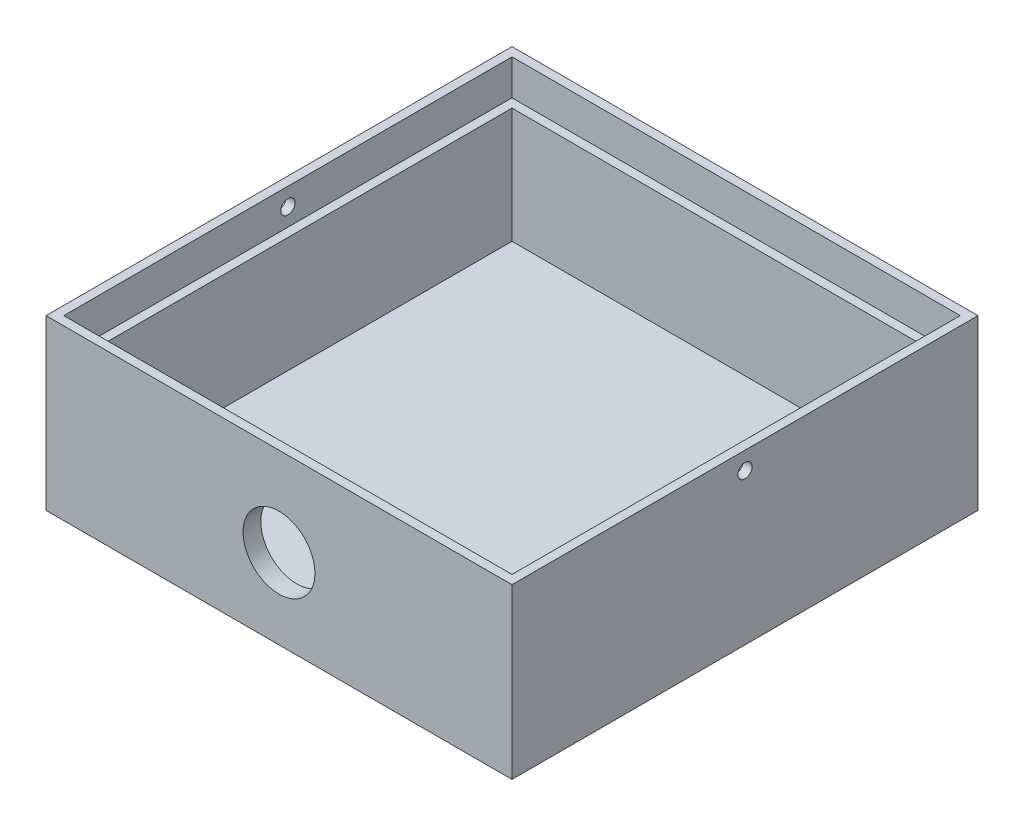
SolidWorks part; units mm, degrees
ref_plane "Front Plane" through (0, 0, 0) normal (0, 0, 1) x (1, 0, 0)
ref_plane "Top Plane" through (0, 0, 0) normal (0, 1, 0) x (1, 0, 0)
ref_plane "Right Plane" through (0, 0, 0) normal (1, 0, 0) x (0, 0, -1)
sketch "Sketch1" plane through (0, 0, 0) normal (0, 1, 0) x (1, 0, 0)
  line L1 (-52.5, 52.5) -> (52.5, 52.5)
  line L2 (-52.5, 52.5) -> (-52.5, -52.5)
  line L3 (-52.5, -52.5) -> (52.5, -52.5)
  line L4 (52.5, 52.5) -> (52.5, -52.5)
  line L5 (-52.5, 52.5) -> (52.5, -52.5) construction
  line L6 (-52.5, -52.5) -> (52.5, 52.5) construction
  point P0 (0, 0)
  dimension "D1" = 105
  dimension "D2" = 105
extrude "Boss-Extrude1" add sketch "Sketch1" along normal blind 38
sketch "Sketch2" plane through (0, 38, 0) normal (0, 1, 0) x (1, 0, 0)
  line L0 (-52.5, 52.5) -> (-52.5, -52.5) construction
  line L1 (-48.5, 48.5) -> (48.5, 48.5)
  line L2 (-48.5, 48.5) -> (-48.5, -48.5)
  line L3 (-48.5, -48.5) -> (48.5, -48.5)
  line L4 (48.5, 48.5) -> (48.5, -48.5)
  line L5 (-48.5, 48.5) -> (48.5, -48.5) construction
  line L6 (-48.5, -48.5) -> (48.5, 48.5) construction
  line L7 (52.5, 52.5) -> (-52.5, 52.5) construction
  point P0 (0, 0)
  dimension "D1" = 4
  dimension "D2" = 4
extrude "Cut-Extrude1" cut sketch "Sketch2" against normal blind 34
sketch "Sketch3" plane through (0, 38, 0) normal (0, 1, 0) x (1, 0, 0)
  line L0 (-52.5, 52.5) -> (-52.5, -52.5) construction
  line L1 (-50.5, 50.5) -> (50.5, 50.5)
  line L2 (-50.5, 50.5) -> (-50.5, -50.5)
  line L3 (-50.5, -50.5) -> (50.5, -50.5)
  line L4 (50.5, 50.5) -> (50.5, -50.5)
  line L5 (-50.5, 50.5) -> (50.5, -50.5) construction
  line L6 (-50.5, -50.5) -> (50.5, 50.5) construction
  line L7 (52.5, 52.5) -> (-52.5, 52.5) construction
  point P0 (0, 0)
  dimension "D1" = 2
  dimension "D2" = 2
extrude "Cut-Extrude2" cut sketch "Sketch3" against normal blind 8
sketch "Sketch5" plane through (52.5, 0, 0) normal (1, 0, 0) x (0, 0, -1)
  line L0 (-52.5, 38) -> (52.5, 38) construction
  circle A0 centre (0, 34) radius 1.6
  dimension "D1" = 3.2
  dimension "D2" = 4
extrude "Cut-Extrude3" cut sketch "Sketch5" against normal through all
sketch "Sketch6" plane through (0, 0, -52.5) normal (0, 0, -1) x (-1, 0, 0)
  line L0 (-52.5, 0) -> (52.5, 0) construction
  line L1 (-12, 0) -> (12, 0)
  line L2 (-12, 0) -> (-12, -5)
  line L4 (12, 0) -> (12, -5)
  line L5 (-52.5, 38) -> (-52.5, 0) construction
  line L8 (-12, -5) -> (-12, -17)
  line L10 (12, -5) -> (12, -17)
  arc A0 (-12, -17) -> (12, -17) centre (0, -17) ccw
  circle A1 centre (0, -17) radius 2.75
  dimension "D5" = 5.5
  dimension "D1" = 5
  dimension "D2" = 24
  dimension "D3" = 40.5
  dimension "D4" = 12
extrude "Boss-Extrude2" add sketch "Sketch6" against normal blind 3
fillet "Fillet1" radius 4 3 edges at (-12, 0, -51) (12, 0, -51) (0, 0, -49.5)
sketch "Sketch7" plane through (0, 0, 48.5) normal (0, 0, -1) x (-1, 0, 0)
  line L0 (-48.5, 30) -> (48.5, 30) construction
  circle A0 centre (0, 18) radius 8.1
  dimension "D1" = 16.2
  dimension "D2" = 12
extrude "Cut-Extrude4" cut sketch "Sketch7" against normal up to next
sketch "Sketch10" plane through (0, 0, 0) normal (0, -1, 0) x (1, 0, 0)
  line L1 (5, -10) -> (0, -10)
  line L2 (5, -10) -> (5, 10)
  line L3 (5, 10) -> (0, 10)
  line L5 (0, -7) -> (2, -7)
  line L7 (0, -3) -> (2, -3)
  line L8 (2, -7) -> (2, -3)
  line L9 (0, 3) -> (2, 3)
  line L11 (0, 7) -> (2, 7)
  line L12 (2, 3) -> (2, 7)
  arc A0 (0, 0) -> (0, -10) centre (0, -5) ccw
  arc A1 (0, 10) -> (0, 0) centre (0, 5) ccw
  arc A2 (0, -3) -> (0, -7) centre (0, -5) ccw
  arc A3 (0, 7) -> (0, 3) centre (0, 5) ccw
  dimension "D3" = 10
  dimension "D4" = 10
  dimension "D5" = 4
  dimension "D6" = 4
  dimension "D1" = 5
  dimension "D2" = 20
  dimension "D7" = 4
  dimension "D8" = 2
  dimension "D9" = 2
  dimension "D10" = 4
extrude "Cut-Extrude5" cut sketch "Sketch10" against normal blind 1
